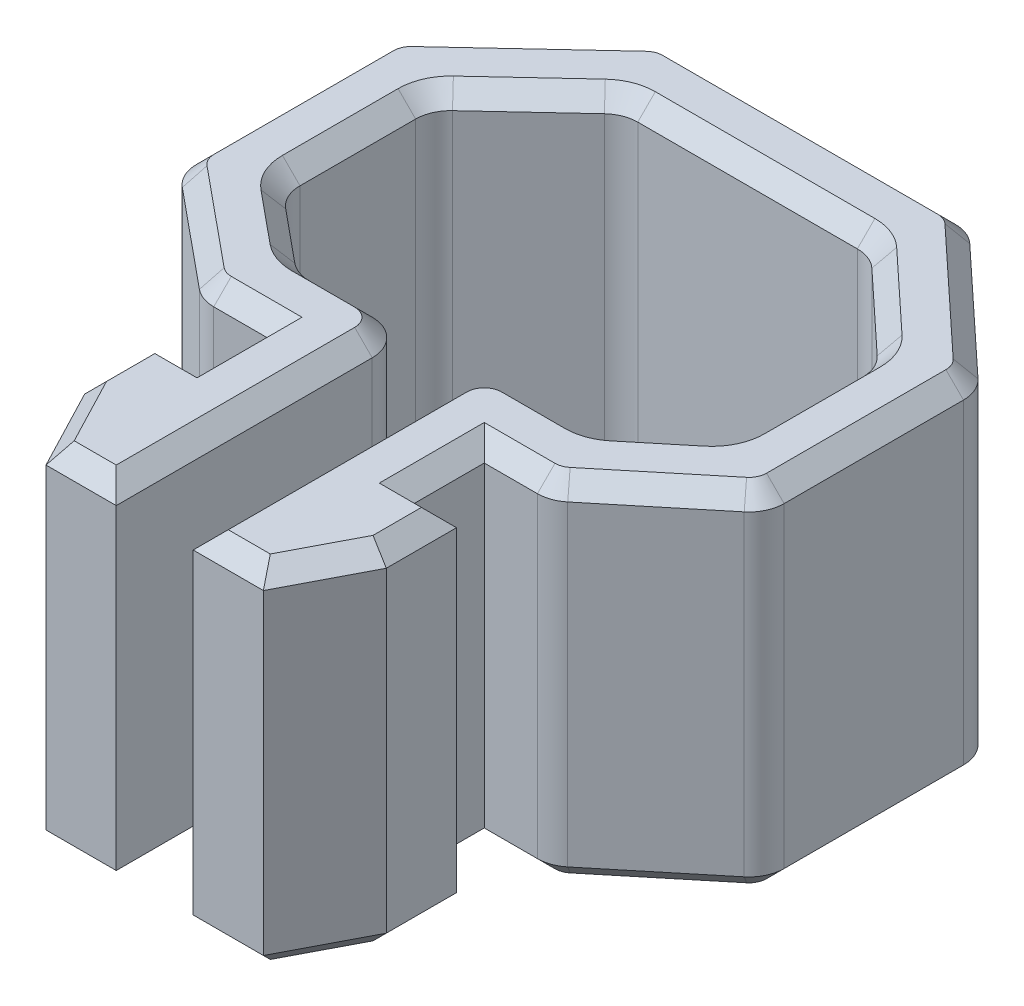
SolidWorks part; units mm, degrees
ref_plane "Front Plane" through (0, 0, 0) normal (0, 0, 1) x (1, 0, 0)
ref_plane "Top Plane" through (0, 0, 0) normal (0, 1, 0) x (1, 0, 0)
ref_plane "Right Plane" through (0, 0, 0) normal (1, 0, 0) x (0, 0, -1)
sketch "Sketch1" plane through (0, 0, 0) normal (0, 1, 0) x (1, 0, 0)
  line L16 (2.19, 0) -> (4.19, 0)
  line L19 (4.19, 4.3) -> (5.39, 4.3)
  line L20 (5.39, 4.3) -> (5.39, 2.3)
  line L21 (5.39, 2.3) -> (4.19, 0)
  line L24 (4.19, 6.29) -> (4.19, 4.3)
  line L49 (2.19, 8.29) -> (2.19, 0)
  line L60 (7.4601, 14.2306) -> (4.6149, 16.8823)
  line L63 (7.4601, 10.0306) -> (5.345, 8.29)
  line L65 (7.4601, 14.2306) -> (7.4601, 10.0306)
  line L66 (5.345, 8.29) -> (2.19, 8.29)
  line L69 (9.4601, 9.0863) -> (6.0621, 6.29)
  line L72 (9.4601, 15.1006) -> (5.4024, 18.8823)
  line L82 (9.4601, 15.1006) -> (9.4601, 9.0863)
  line L83 (6.0621, 6.29) -> (4.19, 6.29)
  line L102 (-3.8721, 6.29) -> (-2, 6.29)
  line L103 (-7.2701, 15.1006) -> (-7.2701, 9.0863)
  line L104 (-7.2701, 15.1006) -> (-3.2124, 18.8823)
  line L105 (-7.2701, 9.0863) -> (-3.8721, 6.29)
  line L106 (-3.155, 8.29) -> (0, 8.29)
  line L107 (-5.2701, 14.2306) -> (-5.2701, 10.0306)
  line L108 (-5.2701, 10.0306) -> (-3.155, 8.29)
  line L109 (-5.2701, 14.2306) -> (-2.4249, 16.8823)
  line L110 (0, 8.29) -> (0, 0)
  line L111 (-2, 6.29) -> (-2, 4.3)
  line L112 (-3.2, 2.3) -> (-2, 0)
  line L113 (-3.2, 4.3) -> (-3.2, 2.3)
  line L114 (-2, 4.3) -> (-3.2, 4.3)
  line L115 (0, 0) -> (-2, 0)
  line L116 (-2.4249, 16.8823) -> (4.6149, 16.8823)
  line L117 (-3.2124, 18.8823) -> (5.4024, 18.8823)
  dimension "D4" = 1.2
  dimension "D5" = 2
  dimension "D6" = 1.8721
  dimension "D7" = 2
  dimension "D8" = 8.29
  dimension "D9" = 2.3
  dimension "D10" = 8.5923
  dimension "D11" = 12.7303
  dimension "D12" = 2
  dimension "D13" = 8.6148
  dimension "D14" = 7.0398
  dimension "D15" = 2
  dimension "D16" = 4.4007
  dimension "D17" = 2.7393
  dimension "D18" = 2
  dimension "D19" = 140.548
  dimension "D20" = 140.548
  dimension "D21" = 90
  dimension "D22" = 90
  dimension "D23" = 90
  dimension "D24" = 2
  dimension "D25" = 152.447
  dimension "D26" = 117.553
  dimension "D27" = 90
  dimension "D28" = 90
  dimension "D29" = 129.452
  dimension "D30" = 129.452
  dimension "D32" = 4.2
  dimension "D34" = 2
  dimension "D35" = 2
extrude "Boss-Extrude1" add sketch "Sketch1" along normal blind 10 contours L49 L16 L21 L20 L19 L24 L83 L69 L82 L72 L117 L104 L103 L105 L102 L111 L114 L113 L112 L115 L110 L106 L108 L107 L109 L116 L60 L65 L63 L66
fillet "Fillet1" radius 1 18 edges at (9.4601, 5, -15.1006) (9.4601, 5, -9.0863) (6.0621, 5, -6.29) (2.19, 5, -8.29) (5.345, 5, -8.29) (7.4601, 5, -10.0306) (7.4601, 5, -14.2306) (-7.2701, 5, -9.0863) (-3.8721, 5, -6.29) (0, 5, -8.29) (-3.155, 5, -8.29) (-5.2701, 5, -10.0306) (-7.2701, 5, -15.1006) (-3.2124, 5, -18.8823) (-5.2701, 5, -14.2306) (-2.4249, 5, -16.8823) (4.6149, 5, -16.8823) (5.4024, 5, -18.8823)
chamfer "Chamfer1" distance 0.5 angle 45 96 edges at (-3.8511, 0, -6.3487) (-2.7568, 0, -6.29) (-2, 0, -5.295) (-2.6, 0, -4.3) (-3.2, 0, -3.3) (-2.6, 0, -1.15) (-1, 0, 0) (0, 0, -3.645) (-0.2929, 0, -7.9971) (-1.8982, 0, -8.29) (-3.134, 0, -8.3487) (-4.1687, 0, -9.1242) (-5.1744, 0, -10.0758) (-5.2701, 0, -12.1492) (-5.1872, 0, -14.1945) (-3.8324, 0, -15.5705) (-2.3975, 0, -16.8128) (1.095, 0, -16.8823) (4.5875, 0, -16.8128) (6.0224, 0, -15.5705) (7.3772, 0, -14.1945) (7.4601, 0, -12.1492) (7.3644, 0, -10.0758) (6.3587, 0, -9.1242) (5.324, 0, -8.3487) (4.0882, 0, -8.29) (2.4829, 0, -7.9971) (2.19, 0, -3.645) (3.19, 0, 0) (4.79, 0, -1.15) (5.39, 0, -3.3) (4.79, 0, -4.3) (4.19, 0, -5.295) (4.9468, 0, -6.29) (6.0411, 0, -6.3487) (7.7173, 0, -7.6521) (9.3644, 0, -9.1315) (9.4601, 0, -12.112) (9.3772, 0, -15.0645) (7.4162, 0, -17.0055) (5.375, 0, -18.8128) (1.095, 0, -18.8823) (-3.185, 0, -18.8128) (-5.2262, 0, -17.0055) (-7.1872, 0, -15.0645) (-7.2701, 0, -12.112) (-7.1744, 0, -9.1315) (-5.5273, 0, -7.6521) (-7.1872, 10, -15.0645) (-5.2262, 10, -17.0055) (-3.185, 10, -18.8128) (1.095, 10, -18.8823) (5.375, 10, -18.8128) (7.4162, 10, -17.0055) (9.3772, 10, -15.0645) (9.4601, 10, -12.112) (9.3644, 10, -9.1315) (7.7173, 10, -7.6521) (6.0411, 10, -6.3487) (4.9468, 10, -6.29) (4.19, 10, -5.295) (4.79, 10, -4.3) (5.39, 10, -3.3) (4.79, 10, -1.15) (3.19, 10, 0) (2.19, 10, -3.645) (2.4829, 10, -7.9971) (4.0882, 10, -8.29) (5.324, 10, -8.3487) (6.3587, 10, -9.1242) (7.3644, 10, -10.0758) (7.4601, 10, -12.1492) (7.3772, 10, -14.1945) (6.0224, 10, -15.5705) (4.5875, 10, -16.8128) (1.095, 10, -16.8823) (-2.3975, 10, -16.8128) (-3.8324, 10, -15.5705) (-5.1872, 10, -14.1945) (-5.2701, 10, -12.1492) (-5.1744, 10, -10.0758) (-4.1687, 10, -9.1242) (-3.134, 10, -8.3487) (-1.8982, 10, -8.29) (-0.2929, 10, -7.9971) (0, 10, -3.645) (-1, 10, 0) (-2.6, 10, -1.15) (-3.2, 10, -3.3) (-2.6, 10, -4.3) (-2, 10, -5.295) (-2.7568, 10, -6.29) (-3.8511, 10, -6.3487) (-5.5273, 10, -7.6521) (-7.1744, 10, -9.1315) (-7.2701, 10, -12.112)
